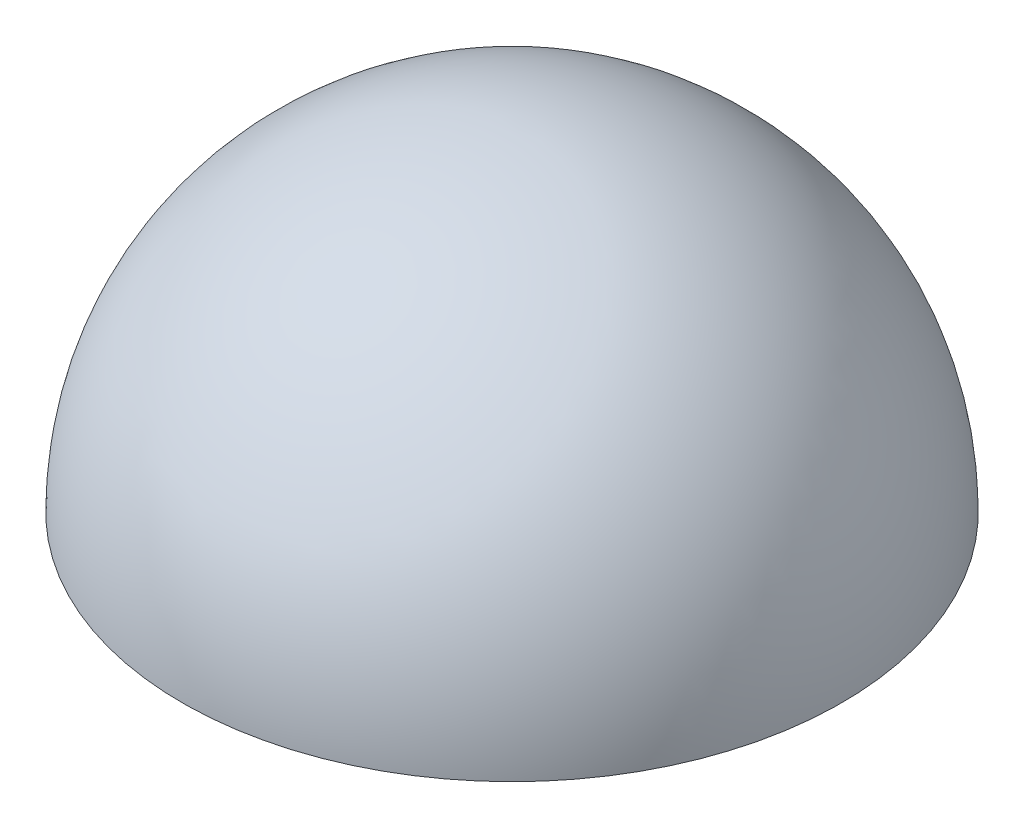
SolidWorks part; units mm, degrees
material "Melamine resin"
ref_plane "Front Plane" through (0, 0, 0) normal (0, 0, 1) x (1, 0, 0)
ref_plane "Top Plane" through (0, 0, 0) normal (0, 1, 0) x (1, 0, 0)
ref_plane "Right Plane" through (0, 0, 0) normal (1, 0, 0) x (0, 0, -1)
sketch "Sketch1" plane through (0, 0, 0) normal (0, 1, 0) x (1, 0, 0)
  line L0 (1.4917, 54.9798) -> (-1.4917, -54.9798)
  arc A0 (-1.4917, -54.9798) -> (1.4917, 54.9798) centre (0, 0) ccw
  dimension "D1" = 110
revolve "Revolve1" add sketch "Sketch1" angle 180 about L0
sketch "Sketch2" plane through (0, 0, 0) normal (0, -1, 0) x (1, 0, 0)
  line L0 (49.9807, 1.3894) -> (-49.9807, -1.3894)
  arc A0 (49.9807, 1.3894) -> (-49.9807, -1.3894) centre (0, 0) ccw
  dimension "D1" = 100
revolve "Cut-Revolve1" cut sketch "Sketch2" angle 360 about L0
sketch "Sketch4" plane through (0, 0, 0) normal (0, -1, 0) x (1, 0, 0)
  circle A0 centre (0, 0) radius 50
  dimension "D1" = 100
extrude "Boss-Extrude1" add sketch "Sketch4" against normal blind 7
sketch "Sketch5" plane through (0, 0, 0) normal (0, -1, 0) x (1, 0, 0)
  circle A2 centre (0, 35) radius 4
  circle A3 centre (30.3109, -17.5) radius 4
  circle A4 centre (-30.3109, -17.5) radius 4
  circle A5 centre (-30.3109, -17.5) radius 1.5
  circle A6 centre (30.3109, -17.5) radius 1.5
  circle A7 centre (0, 35) radius 1.5
  dimension "D2" = 8
  dimension "D3" = 8
  dimension "D4" = 8
  dimension "D8" = 3
  dimension "D9" = 3
  dimension "D10" = 3
  dimension "D5" = 60.6218
  dimension "D6" = 60.6218
  dimension "D7" = 60.6218
extrude "Boss-Extrude2" add sketch "Sketch5" along normal blind 10
sketch "Sketch6" plane through (0, 0, 0) normal (0, -1, 0) x (1, 0, 0)
  circle A0 centre (0, 0) radius 27.5
  dimension "D1" = 55
extrude "Cut-Extrude1" cut sketch "Sketch6" against normal blind 10
sketch "Sketch7" plane through (0, 0, 0) normal (0, -1, 0) x (1, 0, 0)
  line L5 (-29.5963, 3) -> (-6.8739, 3)
  line L6 (-29.5963, 3) -> (-29.5963, -3)
  line L7 (-29.5963, -3) -> (-6.8739, -3)
  line L8 (29.2606, 3) -> (29.2606, -3)
  line L9 (3, 29.0761) -> (-3, 29.0761)
  line L10 (3, 29.0761) -> (3, 6.8739)
  line L11 (3, -30.683) -> (-3, -30.683)
  line L12 (-3, 29.0761) -> (-3, 6.8739)
  line L13 (6.8739, 3) -> (29.2606, 3)
  line L14 (6.8739, -3) -> (29.2606, -3)
  line L15 (3, -6.8739) -> (3, -30.683)
  line L16 (-3, -6.8739) -> (-3, -30.683)
  arc A1 (-3, 6.8739) -> (-6.8739, 3) centre (0, 0) ccw
  arc A2 (6.8739, 3) -> (3, 6.8739) centre (0, 0) ccw
  arc A3 (3, -6.8739) -> (6.8739, -3) centre (0, 0) ccw
  arc A4 (-6.8739, -3) -> (-3, -6.8739) centre (0, 0) ccw
  dimension "D5" = 15
extrude "Boss-Extrude3" add sketch "Sketch7" against normal blind 7
sketch "Sketch8" plane through (0, 0, 0) normal (0, -1, 0) x (1, 0, 0)
  circle A0 centre (0, 0) radius 3
  dimension "D1" = 6
extrude "Boss-Extrude4" add sketch "Sketch8" along normal blind 15
sketch "Sketch9" plane through (0, 0, 0) normal (0, -1, 0) x (1, 0, 0)
  line L4 (1, 1) -> (4.3, 1)
  line L5 (-1, 4.3) -> (1, 4.3)
  line L6 (-1, 4.3) -> (-1, 1)
  line L7 (-1, -4.3) -> (1, -4.3)
  line L8 (1, 4.3) -> (1, 1)
  line L9 (-4.3, 1) -> (-1, 1)
  line L10 (-4.3, 1) -> (-4.3, -1)
  line L11 (-4.3, -1) -> (-1, -1)
  line L12 (4.3, 1) -> (4.3, -1)
  line L14 (1, -1) -> (4.3, -1)
  line L15 (1, -1) -> (1, -4.3)
  line L16 (-1, -1) -> (-1, -4.3)
  dimension "D1" = 8.6
  dimension "D2" = 2
  dimension "D3" = 8.6
  dimension "D4" = 4.3
  dimension "D5" = 2
  dimension "D6" = 4.3
  dimension "D7" = 2
extrude "Boss-Extrude5" add sketch "Sketch9" along normal blind 10
